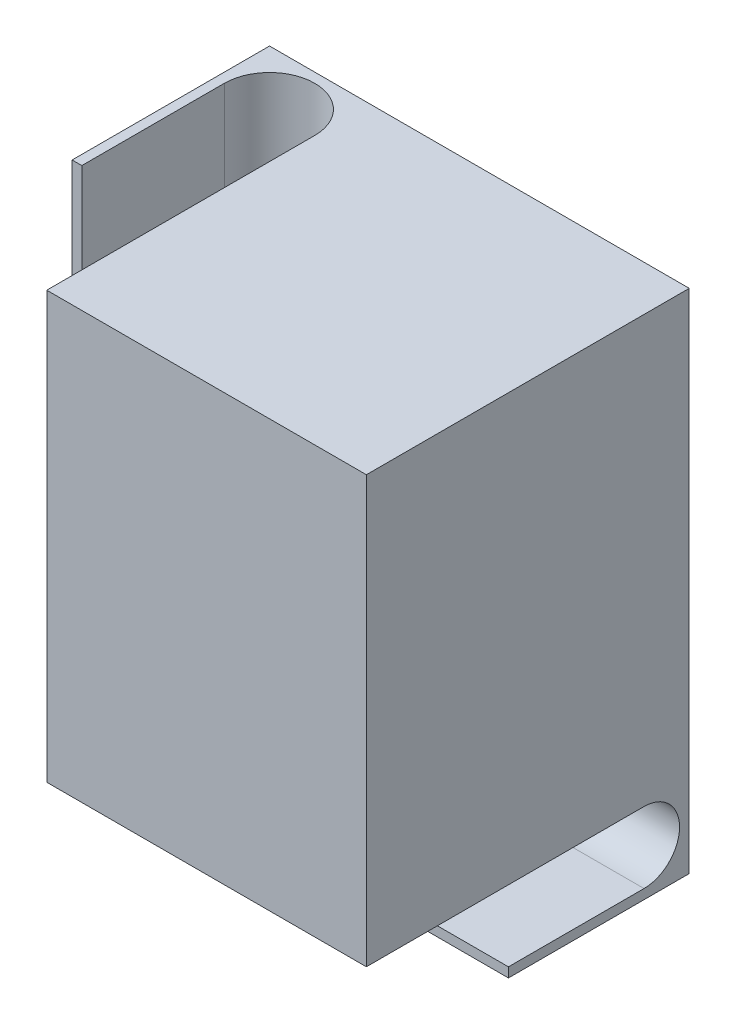
SolidWorks part; units mm, degrees
ref_plane "Front Plane" through (0, 0, 0) normal (0, 0, 1) x (1, 0, 0)
ref_plane "Top Plane" through (0, 0, 0) normal (0, 1, 0) x (1, 0, 0)
ref_plane "Right Plane" through (0, 0, 0) normal (1, 0, 0) x (0, 0, -1)
sketch "Sketch1" plane through (0, 0, 0) normal (0, 0, 1) x (1, 0, 0)
  line L1 (24.5098, 56.8627) -> (154.5098, 56.8627)
  line L2 (24.5098, 56.8627) -> (24.5098, -100.1373)
  line L3 (24.5098, -100.1373) -> (154.5098, -100.1373)
  line L4 (154.5098, 56.8627) -> (154.5098, -100.1373)
  dimension "D1" = 130
  dimension "D2" = 157
extrude "Boss-Extrude1" add sketch "Sketch1" along normal blind 100
sketch "Sketch3" plane through (154.5098, 0, 0) normal (1, 0, 0) x (0, 0, -1)
  line L0 (0, 56.8627) -> (-56, 56.8627) construction
  line L7 (-100, -100.1373) -> (0, -100.1373) construction
  line L8 (-3, -86.1373) -> (-3, 4.8239) construction
  line L10 (0, -100.1373) -> (0, 56.8627) construction
  line L11 (-100, 56.8627) -> (0, 56.8627) construction
  line L13 (-14, -97.1373) -> (-56, -97.1373)
  line L15 (-56, -97.1373) -> (-56, -100.1373)
  line L16 (-14, -75.1373) -> (-100, -75.1373)
  line L17 (-100, -100.1373) -> (-100, 56.8627) construction
  line L18 (-100, -75.1373) -> (-100, -100.1373)
  line L19 (-100, -100.1373) -> (-56, -100.1373)
  arc A1 (-14, -97.1373) -> (-14, -75.1373) centre (-14, -86.1373) ccw
  dimension "D2" = 3
  dimension "D1" = 22
  dimension "D3" = 3
  dimension "D4" = 56
extrude "Cut-Extrude3" cut sketch "Sketch3" against normal up to surface (130 mm away) up to face at (24.5098, -21.6373, 50)
sketch "Sketch9" plane through (0, 56.8627, 0) normal (0, 1, 0) x (1, 0, 0)
  line L0 (27.5098, -17) -> (27.5098, -61.1392)
  line L1 (27.5098, -61.1392) -> (24.5098, -61.1392)
  line L2 (24.5098, -100) -> (24.5098, 0) construction
  line L3 (24.5098, -61.1392) -> (24.5098, -100)
  line L4 (55.5098, -17) -> (55.5098, -100)
  line L5 (154.5098, -100) -> (24.5098, -100) construction
  line L6 (55.5098, -100) -> (24.5098, -100)
  line L7 (41.5098, -3) -> (150.2086, -3) construction
  line L8 (154.5098, 0) -> (24.5098, 0) construction
  arc A0 (55.5098, -17) -> (27.5098, -17) centre (41.5098, -17) ccw
  dimension "D1" = 3
  dimension "D3" = 28
  dimension "D2" = 3
extrude "Cut-Extrude7" cut sketch "Sketch9" against normal up to surface (157 mm away) up to face at (89.5098, -100.1373, 28)
sketch "Sketch10" plane through (0, -100.1373, 0) normal (0, -1, 0) x (1, 0, 0)
  line L0 (55.5098, 3) -> (24.5098, 3)
  line L1 (24.5098, 56) -> (24.5098, 0) construction
  line L2 (24.5098, 3) -> (24.5098, 61.1392)
  line L3 (24.5098, 61.1392) -> (55.5098, 61.1392)
  line L4 (55.5098, 100) -> (55.5098, 17) construction
  line L5 (55.5098, 61.1392) -> (55.5098, 3)
extrude "Cut-Extrude8" cut sketch "Sketch10" against normal up to surface (25 mm away) up to face at (26.3586, -75.1373, 33.4539)
sketch "Sketch11" plane through (0, 0, 0) normal (0, 0, -1) x (-1, 0, 0)
  line L0 (-154.5098, -100.1373) -> (-154.5098, 56.8627) construction
  line L1 (-151.5098, 53.8627) -> (-58.5098, 53.8627)
  line L2 (-151.5098, 53.8627) -> (-151.5098, -72.1373)
  line L3 (-151.5098, -72.1373) -> (-58.5098, -72.1373)
  line L4 (-58.5098, 53.8627) -> (-58.5098, -72.1373)
  line L5 (-154.5098, 56.8627) -> (-24.5098, 56.8627) construction
  line L6 (-55.5098, -75.1373) -> (-154.5098, -75.1373) construction
  line L7 (-55.5098, -75.1373) -> (-55.5098, 56.8627) construction
  dimension "D1" = 3
  dimension "D2" = 3
  dimension "D3" = 3
  dimension "D4" = 3
extrude "Cut-Extrude9" cut sketch "Sketch11" against normal offset from surface (97 mm away) 3 up to face at (105.0098, -9.1373, 100)
